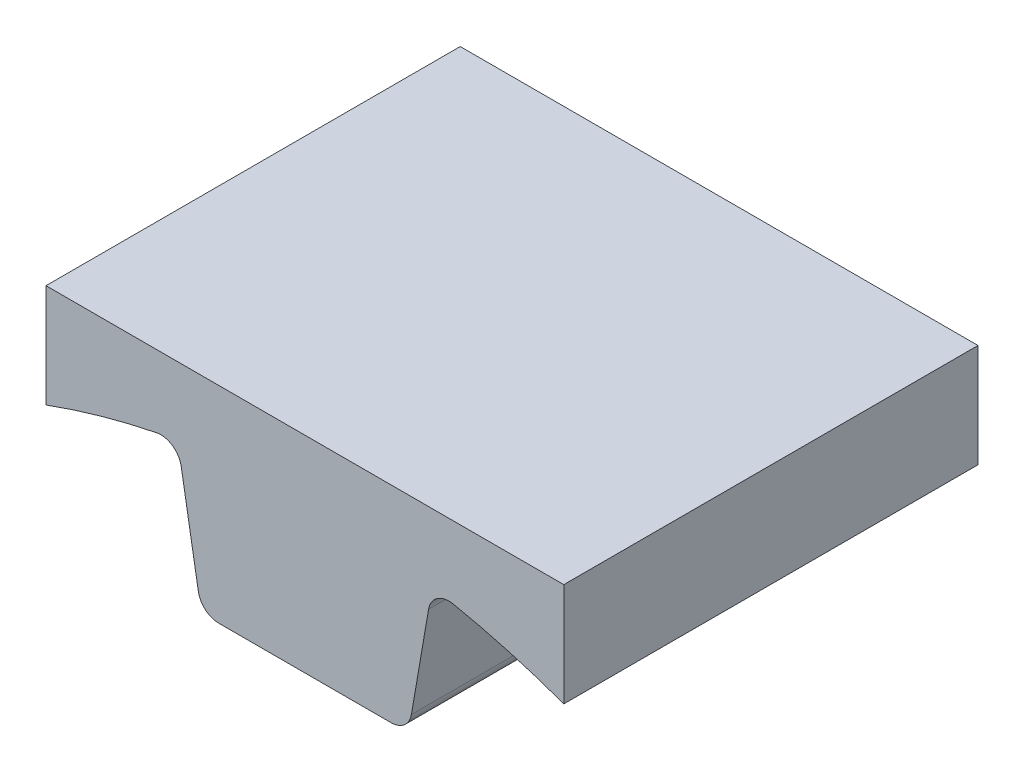
SolidWorks part; units mm, degrees
ref_plane "Front Plane" through (0, 0, 0) normal (0, 0, 1) x (1, 0, 0)
ref_plane "Top Plane" through (0, 0, 0) normal (0, 1, 0) x (1, 0, 0)
ref_plane "Right Plane" through (0, 0, 0) normal (1, 0, 0) x (0, 0, -1)
sketch "Sketch1" plane through (0, 0, 0) normal (0, 0, 1) x (1, 0, 0)
  line L0 (0, 0) -> (0, 112.4335) construction
  line L1 (-12.7, 73.8463) -> (12.7, 73.8463)
  line L2 (12.7, 73.8463) -> (15.6058, 90.7428)
  line L3 (-31.75, 99.1023) -> (31.75, 99.1023)
  line L4 (31.75, 99.1023) -> (31.75, 86.4277)
  line L5 (-31.75, 99.1023) -> (-31.75, 86.4277)
  line L6 (-12.7, 73.8463) -> (-15.6058, 90.7428)
  circle A0 centre (0, 0) radius 92.075 construction
  arc A1 (31.75, 86.4277) -> (15.6058, 90.7428) centre (0, 0) ccw
  arc A2 (-31.75, 86.4277) -> (-15.6058, 90.7428) centre (0, 0) cw
  point P12 (0, 99.1023)
  point P15 (0, 73.8463)
  dimension "D1" = 184.15
  dimension "D2" = 12.7
  dimension "D3" = 17.1446
  dimension "D4" = 31.75
  dimension "D5" = 12.6746
extrude "Boss-Extrude1" add sketch "Sketch1" along normal blind 50.8
fillet "Fillet1" radius 2.54 4 edges at (-15.6058, 90.7428, 25.4) (-12.7, 73.8463, 25.4) (12.7, 73.8463, 25.4) (15.6058, 90.7428, 25.4)
